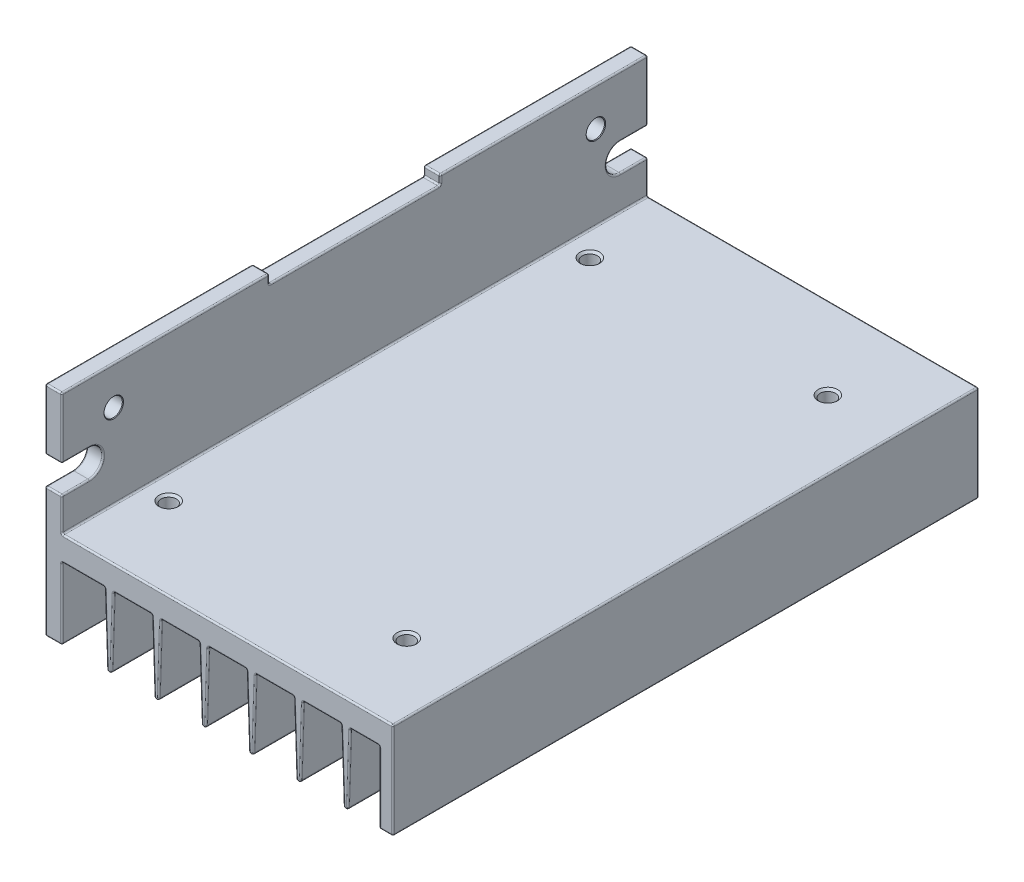
SolidWorks part; units mm, degrees
material "AlMgSi0.5-T4 (6060)"
ref_plane "Front Plane" through (0, 0, 0) normal (0, 0, 1) x (1, 0, 0)
ref_plane "Top Plane" through (0, 0, 0) normal (0, 1, 0) x (1, 0, 0)
ref_plane "Right Plane" through (0, 0, 0) normal (1, 0, 0) x (0, 0, -1)
sketch "Body Profile Sketch" plane through (0, 0, 0) normal (0, 0, 1) x (1, 0, 0)
  line L43 (0.25, 0) -> (54, 0)
  line L44 (54.25, -0.25) -> (54.25, -15.5)
  line L50 (54, -15.75) -> (52.25, -15.75)
  line L51 (52, -15.5) -> (52, -4.25)
  line L52 (51.75, -4) -> (47.4919, -4)
  line L53 (0, -4.25) -> (0, -15.5)
  line L54 (-0.25, -15.75) -> (-2.5, -15.75)
  line L55 (-2.75, -15.5) -> (-2.75, 19.75)
  line L56 (-2.5, 20) -> (-0.25, 20)
  line L57 (0, 19.75) -> (0, 0.25)
  line L58 (8.492, -4.2418) -> (8.1248, -15.3873)
  line L59 (7.008, -4.2418) -> (7.3752, -15.3873)
  line L60 (7.75, -4) -> (7.75, -15.75) construction
  line L61 (6.7581, -4) -> (0.25, -4)
  line L62 (8.5, -4) -> (7, -4) construction
  line L63 (16.242, -4.2418) -> (15.8748, -15.3873)
  line L64 (16.25, -4) -> (14.75, -4) construction
  line L65 (15.5, -4) -> (15.5, -15.75) construction
  line L66 (14.758, -4.2418) -> (15.1252, -15.3873)
  line L67 (23.992, -4.2418) -> (23.6248, -15.3873)
  line L68 (24, -4) -> (22.5, -4) construction
  line L69 (23.25, -4) -> (23.25, -15.75) construction
  line L70 (22.508, -4.2418) -> (22.8752, -15.3873)
  line L71 (31.742, -4.2418) -> (31.3748, -15.3873)
  line L72 (31.75, -4) -> (30.25, -4) construction
  line L73 (31, -4) -> (31, -15.75) construction
  line L74 (30.258, -4.2418) -> (30.6252, -15.3873)
  line L75 (39.492, -4.2418) -> (39.1248, -15.3873)
  line L76 (39.5, -4) -> (38, -4) construction
  line L77 (38.75, -4) -> (38.75, -15.75) construction
  line L78 (38.008, -4.2418) -> (38.3752, -15.3873)
  line L79 (47.242, -4.2418) -> (46.8748, -15.3873)
  line L80 (47.25, -4) -> (45.75, -4) construction
  line L81 (46.5, -4) -> (46.5, -15.75) construction
  line L82 (45.758, -4.2418) -> (46.1252, -15.3873)
  line L83 (14.5081, -4) -> (8.7419, -4)
  line L84 (22.2581, -4) -> (16.4919, -4)
  line L85 (30.0081, -4) -> (24.2419, -4)
  line L86 (37.7581, -4) -> (31.9919, -4)
  line L87 (45.5081, -4) -> (39.7419, -4)
  arc A28 (7.3752, -15.3873) -> (8.1248, -15.3873) centre (7.75, -15.375) ccw
  arc A29 (-0.25, 20) -> (0, 19.75) centre (-0.25, 19.75) cw
  arc A30 (-2.75, 19.75) -> (-2.5, 20) centre (-2.5, 19.75) cw
  arc A31 (0.25, 0) -> (0, 0.25) centre (0.25, 0.25) cw
  arc A32 (-2.5, -15.75) -> (-2.75, -15.5) centre (-2.5, -15.5) cw
  arc A33 (0, -15.5) -> (-0.25, -15.75) centre (-0.25, -15.5) cw
  arc A34 (0.25, -4) -> (0, -4.25) centre (0.25, -4.25) ccw
  arc A35 (7.008, -4.2418) -> (6.7581, -4) centre (6.7581, -4.25) ccw
  arc A36 (8.492, -4.2418) -> (8.7419, -4) centre (8.7419, -4.25) cw
  arc A37 (54, 0) -> (54.25, -0.25) centre (54, -0.25) cw
  arc A38 (52, -4.25) -> (51.75, -4) centre (51.75, -4.25) ccw
  arc A39 (54.25, -15.5) -> (54, -15.75) centre (54, -15.5) cw
  arc A40 (52.25, -15.75) -> (52, -15.5) centre (52.25, -15.5) cw
  arc A41 (16.242, -4.2418) -> (16.4919, -4) centre (16.4919, -4.25) cw
  arc A42 (15.1252, -15.3873) -> (15.8748, -15.3873) centre (15.5, -15.375) ccw
  arc A43 (14.758, -4.2418) -> (14.5081, -4) centre (14.5081, -4.25) ccw
  arc A44 (23.992, -4.2418) -> (24.2419, -4) centre (24.2419, -4.25) cw
  arc A45 (22.8752, -15.3873) -> (23.6248, -15.3873) centre (23.25, -15.375) ccw
  arc A46 (22.508, -4.2418) -> (22.2581, -4) centre (22.2581, -4.25) ccw
  arc A47 (31.742, -4.2418) -> (31.9919, -4) centre (31.9919, -4.25) cw
  arc A48 (30.6252, -15.3873) -> (31.3748, -15.3873) centre (31, -15.375) ccw
  arc A49 (30.258, -4.2418) -> (30.0081, -4) centre (30.0081, -4.25) ccw
  arc A50 (39.492, -4.2418) -> (39.7419, -4) centre (39.7419, -4.25) cw
  arc A51 (38.3752, -15.3873) -> (39.1248, -15.3873) centre (38.75, -15.375) ccw
  arc A52 (38.008, -4.2418) -> (37.7581, -4) centre (37.7581, -4.25) ccw
  arc A53 (47.242, -4.2418) -> (47.4919, -4) centre (47.4919, -4.25) cw
  arc A54 (46.1252, -15.3873) -> (46.8748, -15.3873) centre (46.5, -15.375) ccw
  arc A55 (45.758, -4.2418) -> (45.5081, -4) centre (45.5081, -4.25) ccw
  point P11 (7.75, -4)
  point P22 (-2.75, 20)
  point P25 (0, 0)
  point P28 (-2.75, -15.75)
  point P31 (0, -15.75)
  point P34 (0, -4)
  point P47 (54.25, -15.75)
  point P50 (52, -15.75)
  dimension "D7" = 0.375
  dimension "D8" = 1.5
  dimension "D10" = 0.25
  dimension "D11" = 6
  dimension "D1" = 57
  dimension "D2" = 2.25
  dimension "D3" = 4
  dimension "D4" = 2.75
  dimension "D5" = 11.75
  dimension "D6" = 35.75
  dimension "D9" = 7.75
  dimension "D12" = 7.75
extrude "Body" add sketch "Body Profile Sketch" along normal mid plane 96
sketch "Top Cut Out Sketch" plane through (0, 20, 0) normal (0, 1, 0) x (1, 0, 0)
  line L1 (14, -14) -> (-14, -14)
  line L2 (14, -14) -> (14, 14)
  line L3 (14, 14) -> (-14, 14)
  line L4 (-14, -14) -> (-14, 14)
  line L5 (14, -14) -> (-14, 14) construction
  line L6 (14, 14) -> (-14, -14) construction
  point P0 (0, 0)
  dimension "D1" = 28
extrude "Top Cut Out" cut sketch "Top Cut Out Sketch" against normal blind 1.5
sketch "Side Cut Out Sketch" plane through (0, 0, 0) normal (1, 0, 0) x (0, 0, -1)
  line L0 (48, 10) -> (43.5, 10)
  line L1 (48, 5.5) -> (43.5, 5.5)
  line L2 (48, 0.25) -> (48, 19.75) construction
  line L3 (0, 0) -> (0, 23.773) construction
  line L4 (-48, 10) -> (-43.5, 10)
  line L5 (-48, 5.5) -> (-43.5, 5.5)
  line L7 (48, 5.5) -> (48, 10)
  line L8 (-48, 5.5) -> (-48, 10)
  arc A0 (43.5, 10) -> (43.5, 5.5) centre (43.5, 7.75) ccw
  arc A1 (-43.5, 10) -> (-43.5, 5.5) centre (-43.5, 7.75) cw
  dimension "D1" = 87
  dimension "D3" = 2.25
  dimension "D2" = 7.75
extrude "Side Cut Out" cut sketch "Side Cut Out Sketch" against normal through all
hole_wizard "M3 Top Holes" positions "Sketch3" profile "Sketch4" tap size "M3" standard "ISO" end condition through all
sketch "Sketch3" plane through (0, 0, 0) normal (0, 1, 0) x (1, 0, 0)
  line L0 (43, 34.5) -> (4, -34.5) construction
  line L4 (0, -48) -> (0, 48) construction
  point P0 (43, 34.5)
  point P2 (43, -34.5)
  point P4 (4, -34.5)
  point P6 (4, 34.5)
  point P13 (23.5, 0)
  dimension "D1" = 69
  dimension "D2" = 39
  dimension "D3" = 43
sketch "Sketch4" plane through (43, 0, -34.5) normal (1, 0, 0) x (0, 0, 1)
  line L0 (0, 0) -> (0, 4)
  line L1 (0, 4) -> (1.6, 4)
  line L2 (1.25, 3.65) -> (1.25, 0.35)
  line L3 (1.25, 0.35) -> (1.6, 0)
  line L5 (1.6, 0) -> (0, 0)
  line L6 (-1.25, 0.35) -> (-1.6, 0) construction
  line L7 (1.6, 4) -> (1.25, 3.65)
  line L8 (-1.6, 4) -> (-1.25, 3.65) construction
  line L11 (0, -6.35) -> (0, 107.95) construction
  dimension "Thru Tap Drill Dia." = 2.5
  dimension "Thru Tap Drill Depth" = 4
  dimension "Near C'Sink Dia." = 3.2
  dimension "Near C'Sink Angle" = 90
  dimension "Far C'Sink Dia." = 3.2
  dimension "Far C'Sink Angle" = 90
cosmetic thread "Hole Thread1" parameters "D2"=3
cosmetic thread "Hole Thread2" parameters "D2"=3
cosmetic thread "Hole Thread3" parameters "D2"=3
cosmetic thread "Hole Thread4" parameters "D2"=3
hole_wizard "Ø3.0 Side Holes" positions "Sketch5" profile "Sketch6" hole size "Ø3.0" standard "ISO" end condition through all
sketch "Sketch5" plane through (0, 0, 0) normal (1, 0, 0) x (0, 0, -1)
  line L0 (-39.5, 13.75) -> (39.5, 13.75) construction
  point P0 (39.5, 13.75)
  point P2 (-39.5, 13.75)
  point P9 (0, 13.75)
  dimension "D1" = 79
  dimension "D2" = 13.75
sketch "Sketch6" plane through (0, 13.75, -39.5) normal (0, 1, 0) x (0, 0, -1)
  line L0 (0, 0) -> (0, 2.75)
  line L1 (0, 2.75) -> (1.6, 2.75)
  line L2 (1.5, 2.65) -> (1.5, 0.1)
  line L3 (1.5, 0.1) -> (1.6, 0)
  line L5 (1.6, 0) -> (0, 0)
  line L6 (-1.5, 0.1) -> (-1.6, 0) construction
  line L7 (1.6, 2.75) -> (1.5, 2.65)
  line L8 (-1.6, 2.75) -> (-1.5, 2.65) construction
  line L11 (0, -6.35) -> (0, 107.95) construction
  dimension "Thru Hole Dia." = 3
  dimension "Thru Hole Depth" = 2.75
  dimension "Near C'Sink Dia." = 3.2
  dimension "Near C'Sink Angle" = 90
  dimension "Far C'Sink Dia." = 3.2
  dimension "Far C'Sink Angle" = 90
fillet "Production Fillet" radius 0.25 124 edges at (-1.375, 20, -14) (-0.0732, 19.9268, -14) (-2.6768, 19.9268, -14) (-0.0732, 19.9268, 14) (-2.6768, 19.9268, 14) (0, 19.125, -14) (-2.75, 19.125, -14) (0, 19.125, 14) (-2.75, 19.125, 14) (-2.75, 10, -45.75) (-2.75, 7.75, -41.25) (0, 10, -45.75) (0, 7.75, -41.25) (-2.75, 10, 45.75) (-2.75, 7.75, 41.25) (0, 10, 45.75) (0, 7.75, 41.25) (0, 2.875, 48) (0.0732, 0.0732, 48) (27.125, 0, 48) (54.1768, -0.0732, 48) (54.25, -7.875, 48) (54.1768, -15.6768, 48) (53.125, -15.75, 48) (52.0732, -15.6768, 48) (52, -9.875, 48) (51.9268, -4.0732, 48) (49.6209, -4, 48) (47.3181, -4.0703, 48) (46.5, -15.75, 48) (45.9416, -9.8146, 48) (45.6819, -4.0703, 48) (39.5681, -4.0703, 48) (38.1916, -9.8146, 48) (34.875, -4, 48) (31.8181, -4.0703, 48) (31.5584, -9.8146, 48) (31, -15.75, 48) (30.4416, -9.8146, 48) (27.125, -4, 48) (24.0681, -4.0703, 48) (23.8084, -9.8146, 48) (23.25, -15.75, 48) (22.6916, -9.8146, 48) (22.4319, -4.0703, 48) (19.375, -4, 48) (16.3181, -4.0703, 48) (16.0584, -9.8146, 48) (15.5, -15.75, 48) (14.9416, -9.8146, 48) (14.6819, -4.0703, 48) (11.625, -4, 48) (8.5681, -4.0703, 48) (8.3084, -9.8146, 48) (7.1916, -9.8146, 48) (6.9319, -4.0703, 48) (0.0732, -4.0732, 48) (0, -9.875, 48) (-0.0732, -15.6768, 48) (-1.375, -15.75, 48) (-2.6768, -15.6768, 48) (-2.75, -5, -48) (-1.375, -15.75, -48) (-0.0732, -15.6768, -48) (0, -9.875, -48) (0.0732, -4.0732, -48) (3.5041, -4, -48) (6.9319, -4.0703, -48) (7.1916, -9.8146, -48) (7.75, -15.75, -48) (8.5681, -4.0703, -48) (11.625, -4, -48) (14.6819, -4.0703, -48) (14.9416, -9.8146, -48) (15.5, -15.75, -48) (16.0584, -9.8146, -48) (16.3181, -4.0703, -48) (19.375, -4, -48) (22.4319, -4.0703, -48) (22.6916, -9.8146, -48) (23.25, -15.75, -48) (23.8084, -9.8146, -48) (24.0681, -4.0703, -48) (27.125, -4, -48) (30.1819, -4.0703, -48) (31, -15.75, -48) (31.5584, -9.8146, -48) (34.875, -4, -48) (38.75, -15.75, -48) (39.3084, -9.8146, -48) (39.5681, -4.0703, -48) (42.625, -4, -48) (45.6819, -4.0703, -48) (45.9416, -9.8146, -48) (46.5, -15.75, -48) (47.3181, -4.0703, -48) (51.9268, -4.0732, -48) (52, -9.875, -48) (52.0732, -15.6768, -48) (53.125, -15.75, -48) (54.1768, -15.6768, -48) (54.25, -7.875, -48) (54.1768, -0.0732, -48) (27.125, 0, -48) (0, 2.875, -48) (-2.75, 5.5, -45.75) (-1.375, 5.5, -48) (0, 5.5, -45.75) (0, 14.875, -48) (-0.0732, 19.9268, -48) (-1.375, 20, -48) (-2.75, 14.875, -48) (-1.375, 10, -48) (-1.375, 5.5, 48) (-2.6768, 19.9268, 48) (-1.375, 20, 48) (0, 14.875, 48) (-1.375, 10, 48) (-2.75, 14.875, 48) (-1.375, 18.5, -14) (0, 18.5, 0) (-1.375, 18.5, 14) (-2.75, 18.5, 0) (-2.75, -5, 48)
